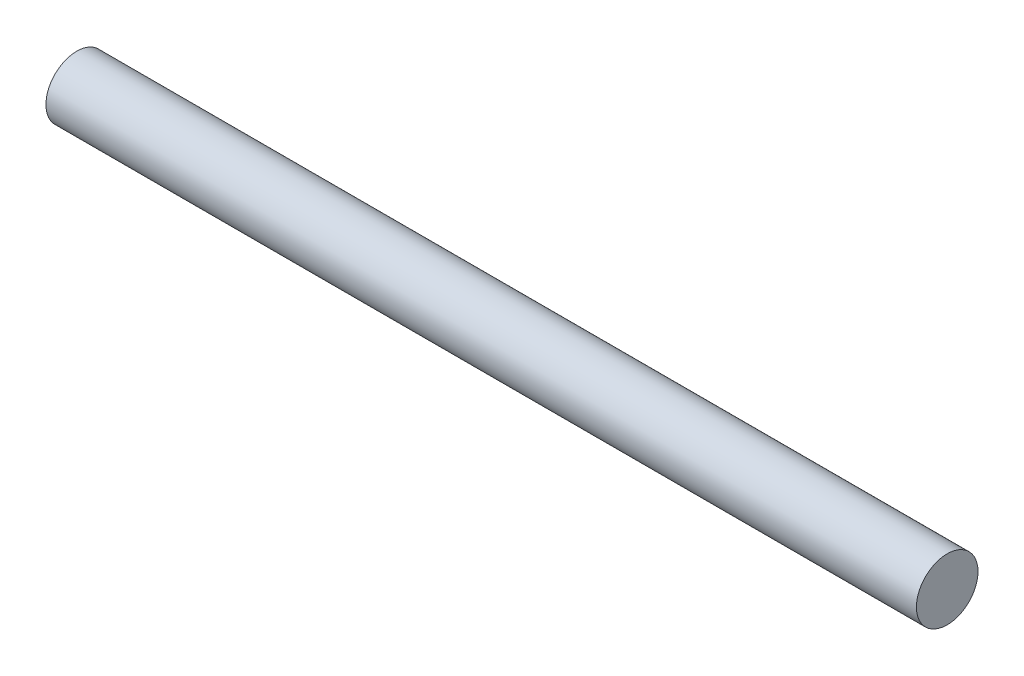
SolidWorks part; units mm, degrees
ref_plane "Front Plane" through (0, 0, 0) normal (0, 0, 1) x (1, 0, 0)
ref_plane "Top Plane" through (0, 0, 0) normal (0, 1, 0) x (1, 0, 0)
ref_plane "Right Plane" through (0, 0, 0) normal (1, 0, 0) x (0, 0, -1)
sketch "Sketch1" plane through (0, 0, 0) normal (1, 0, 0) x (0, 0, -1)
  circle A0 centre (0, 0) radius 1.1684
  dimension "D1" = 2.3368
extrude "Boss-Extrude1" add sketch "Sketch1" along normal blind 33.02
